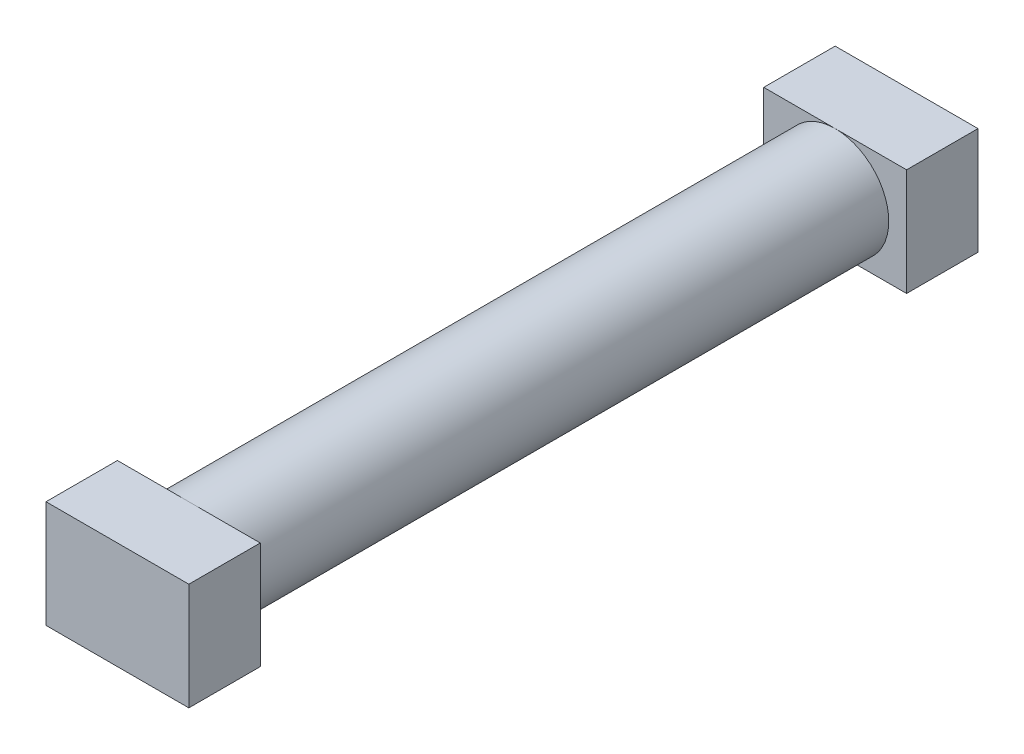
SolidWorks part; units mm, degrees
ref_plane "Front Plane" through (0, 0, 0) normal (0, 0, 1) x (1, 0, 0)
ref_plane "Top Plane" through (0, 0, 0) normal (0, 1, 0) x (1, 0, 0)
ref_plane "Right Plane" through (0, 0, 0) normal (1, 0, 0) x (0, 0, -1)
sketch "Sketch1" plane through (0, 0, 0) normal (0, 0, 1) x (1, 0, 0)
  circle A0 centre (0, 0) radius 1.5
  dimension "D1" = 3
extrude "Boss-Extrude1" add sketch "Sketch1" along normal mid plane 18.1
sketch "Sketch2" plane through (0, 0, 9.05) normal (0, 0, 1) x (1, 0, 0)
  line L1 (-2, 1.5) -> (2, 1.5)
  line L2 (-2, 1.5) -> (-2, -1.5)
  line L3 (-2, -1.5) -> (2, -1.5)
  line L4 (2, 1.5) -> (2, -1.5)
  dimension "D1" = 3
  dimension "D2" = 1.5
  dimension "D3" = 4
  dimension "D4" = 2
extrude "Boss-Extrude2" add sketch "Sketch2" along normal blind 2
sketch "Sketch3" plane through (0, 0, -9.05) normal (0, 0, -1) x (-1, 0, 0)
  line L1 (-2, 1.5) -> (2, 1.5)
  line L2 (-2, 1.5) -> (-2, -1.5)
  line L3 (-2, -1.5) -> (2, -1.5)
  line L4 (2, 1.5) -> (2, -1.5)
extrude "Boss-Extrude3" add sketch "Sketch3" along normal blind 2
